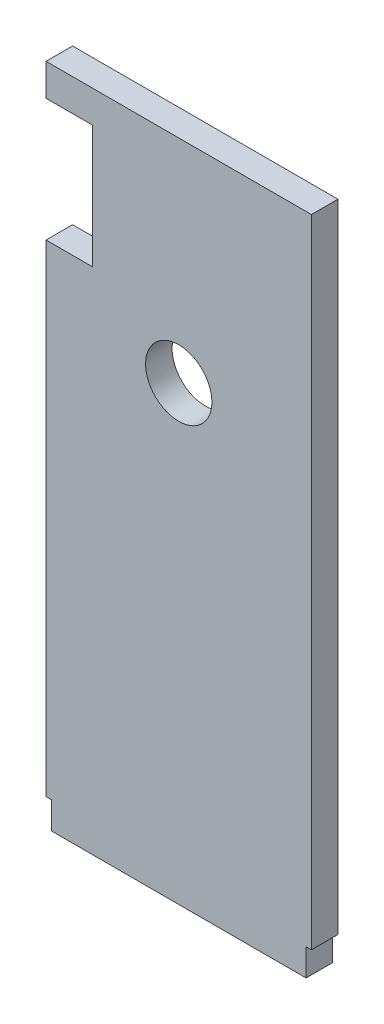
SolidWorks part; units mm, degrees
material "6061 Alloy"
ref_plane "Front Plane" through (0, 0, 0) normal (0, 0, 1) x (1, 0, 0)
ref_plane "Top Plane" through (0, 0, 0) normal (0, 1, 0) x (1, 0, 0)
ref_plane "Right Plane" through (0, 0, 0) normal (1, 0, 0) x (0, 0, -1)
sketch "Sketch2" plane through (0, 0, 0) normal (0, 0, 1) x (1, 0, 0)
  line L0 (31.75, 158.877) -> (31.75, 0) construction
  line L1 (0, 0) -> (63.5, 0)
  line L2 (0, 0) -> (0, 158.877) construction
  line L3 (0, 158.877) -> (63.5, 158.877) construction
  line L4 (63.5, 0) -> (63.5, 158.877)
  line L5 (0, 0) -> (0, 124.3838) construction
  line L6 (3.556, 136.271) -> (59.944, 136.271) construction
  line L7 (3.556, 136.271) -> (3.556, 79.883) construction
  line L8 (3.556, 79.883) -> (59.944, 79.883) construction
  line L9 (59.944, 136.271) -> (59.944, 79.883) construction
  line L10 (3.556, 136.271) -> (59.944, 79.883) construction
  line L11 (3.556, 79.883) -> (59.944, 136.271) construction
  line L12 (0, 158.877) -> (0, 148.6662) construction
  line L13 (0, 148.6662) -> (8.5598, 148.6662) construction
  line L14 (0, 158.877) -> (63.5, 158.877)
  line L15 (8.5598, 148.6662) -> (8.5598, 124.3838) construction
  line L16 (8.5598, 124.3838) -> (0, 124.3838) construction
  line L17 (0, 151.2062) -> (11.0998, 151.2062)
  line L18 (11.0998, 151.2062) -> (11.0998, 121.8438)
  line L19 (11.0998, 121.8438) -> (0, 121.8438)
  line L20 (0, 158.877) -> (0, 151.2062)
  line L22 (0, 121.8438) -> (0, 0)
  circle A0 centre (31.75, 108.077) radius 7.9375
  point P7 (31.75, 108.077)
  dimension "D5" = 15.875
  dimension "D1" = 63.5
  dimension "D2" = 108.077
  dimension "D3" = 56.388
  dimension "D4" = 50.8
  dimension "D6" = 8.5598
  dimension "D7" = 24.2824
  dimension "D8" = 10.2108
  dimension "D9" = 2.54
extrude "Boss-Extrude1" add sketch "Sketch2" along normal blind 6.35
sketch "Sketch3" plane through (0, 0, 6.35) normal (0, 0, 1) x (1, 0, 0)
  line L1 (0, 0) -> (1.27, 0)
  line L2 (0, 0) -> (0, 6.477)
  line L3 (0, 6.477) -> (1.27, 6.477)
  line L4 (1.27, 0) -> (1.27, 6.477)
  line L5 (63.5, 0) -> (62.23, 0)
  line L6 (63.5, 0) -> (63.5, 6.477)
  line L7 (63.5, 6.477) -> (62.23, 6.477)
  line L8 (62.23, 0) -> (62.23, 6.477)
  dimension "D1" = 6.477
  dimension "D2" = 60.96
extrude "Cut-Extrude1" cut sketch "Sketch3" against normal through all
equation "\"base length\"= 21"
equation "\"glass pane length\"= 14.125"
equation "\"glass pane width\"= 10.1875"
equation "\"glass pane wall width\"= 3/4"
equation "\"glass lip\"= 1/4"
equation "\"bolt diameter\"= 0.2"
equation "\"stepper body width\"= 2.22"
equation "\"stepper mount offset\"= 0.19"
equation "\"stepper mount diameter\"= 0.19"
equation "\"stepper shaft offset from body\"= 0.79"
equation "\"stepper spacer thickness\"= 0.2"
equation "\"y axis stepper wall height off base\"= 8"
equation "\"y axis stepper wall bracket thickness\"= 1"
equation "\"y axis stepper wall mount side offset\"= 1/2"
equation "\"y axis stepper wall mount top offset\"= 1/2"
equation "\"y axis stepper wall width\"= \"stepper body width\" + 1                  "
equation "\"thin metal\"= 0.12"
equation "\"thick metal\"= 0.25"
equation "\"recognizer width\"= 2.5"
equation "\"recognizer nut plate height\"= 1.25"
equation "\"recognizer nut plate offset\"= 1.5"
equation "\"D1@Sketch2\"=\"recognizer width\""
equation "\"D2@Sketch2\"  = \"recognizer arm height to hole\""
equation "\"base width\"= 16.5"
equation "\"recognizer arm height to hole\"= 4.255"
equation "\"recognizer bracket length\"= 4"
equation "\"x axis threaded rod length\"= 3"
